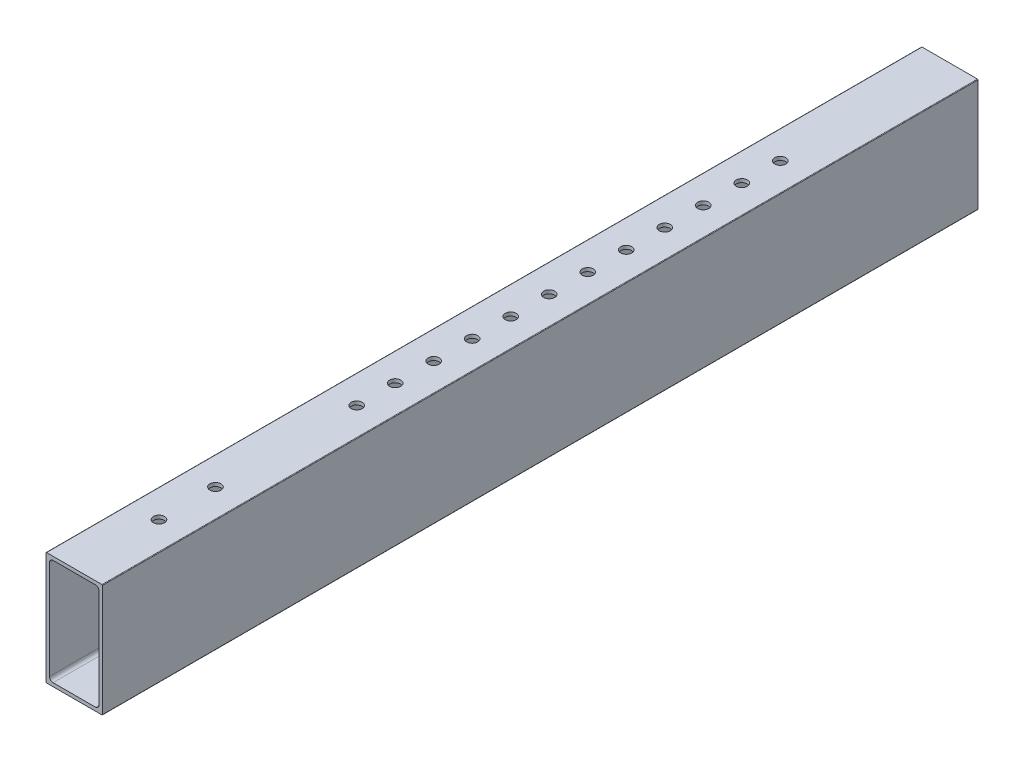
SolidWorks part; units mm, degrees
material "6061 Alloy"
ref_plane "Front Plane" through (0, 0, 0) normal (0, 0, 1) x (1, 0, 0)
ref_plane "Top Plane" through (0, 0, 0) normal (0, 1, 0) x (1, 0, 0)
ref_plane "Right Plane" through (0, 0, 0) normal (1, 0, 0) x (0, 0, -1)
ref_plane "Plane1" through (0, 0, 0) normal (0, 0, -1) x (-1, 0, 0)
sketch "Sketch1" plane through (0, 0, 0) normal (0, 0, -1) x (-1, 0, 0)
  line L0 (-11.1125, -22.225) -> (-11.1125, 22.225)
  line L1 (-9.525, 23.8125) -> (9.525, 23.8125)
  line L2 (11.1125, 22.225) -> (11.1125, -22.225)
  line L3 (9.525, -23.8125) -> (-9.525, -23.8125)
  line L4 (-12.7, 25.146) -> (-12.7, -25.146)
  line L5 (-12.446, -25.4) -> (12.446, -25.4)
  line L6 (12.7, -25.146) -> (12.7, 25.146)
  line L7 (12.446, 25.4) -> (-12.446, 25.4)
  arc A0 (-11.1125, 22.225) -> (-9.525, 23.8125) centre (-9.525, 22.225) cw
  arc A1 (9.525, 23.8125) -> (11.1125, 22.225) centre (9.525, 22.225) cw
  arc A2 (11.1125, -22.225) -> (9.525, -23.8125) centre (9.525, -22.225) cw
  arc A3 (-9.525, -23.8125) -> (-11.1125, -22.225) centre (-9.525, -22.225) cw
  arc A4 (-12.7, -25.146) -> (-12.446, -25.4) centre (-12.446, -25.146) ccw
  arc A5 (12.446, -25.4) -> (12.7, -25.146) centre (12.446, -25.146) ccw
  arc A6 (12.7, 25.146) -> (12.446, 25.4) centre (12.446, 25.146) ccw
  arc A7 (-12.446, 25.4) -> (-12.7, 25.146) centre (-12.446, 25.146) ccw
extrude "Boss-Extrude1" add sketch "Sketch1" against normal blind 393.7 from offset 88.9 offset against normal yes
sketch "Sketch3" plane through (0, -25.4, 0) normal (0, -1, 0) x (1, 0, 0)
  line L0 (0, 0) -> (0, 482.6) construction
  line L1 (12.446, 482.6) -> (-12.446, 482.6) construction
  line L2 (12.446, 88.9) -> (-12.446, 88.9) construction
  line L3 (-12.7, 381) -> (12.7, 381) construction
  line L4 (-12.7, 482.6) -> (-12.7, 88.9) construction
  line L5 (12.7, 482.6) -> (12.7, 88.9) construction
  circle A0 centre (0, 165.1) radius 2.4892
  circle A1 centre (0, 182.4182) radius 2.4892
  circle A2 centre (0, 199.7364) radius 2.4892
  circle A3 centre (0, 217.0545) radius 2.4892
  circle A4 centre (0, 234.3727) radius 2.4892
  circle A5 centre (0, 251.6909) radius 2.4892
  circle A6 centre (0, 269.0091) radius 2.4892
  circle A7 centre (0, 286.3273) radius 2.4892
  circle A8 centre (0, 303.6455) radius 2.4892
  circle A9 centre (0, 320.9636) radius 2.4892
  circle A10 centre (0, 338.2818) radius 2.4892
  circle A11 centre (0, 419.1) radius 2.4892
  circle A12 centre (0, 444.5) radius 2.4892
  circle A13 centre (0, 355.6) radius 2.4892
  dimension "D1" = 76.2
  dimension "D2" = 4.9784
  dimension "D3" = 12
  dimension "D4" = 25.4
  dimension "D7" = 127
  dimension "D5" = 38.1
  dimension "D6" = 101.6
extrude "Cut-Extrude2" cut sketch "Sketch3" against normal through all both
